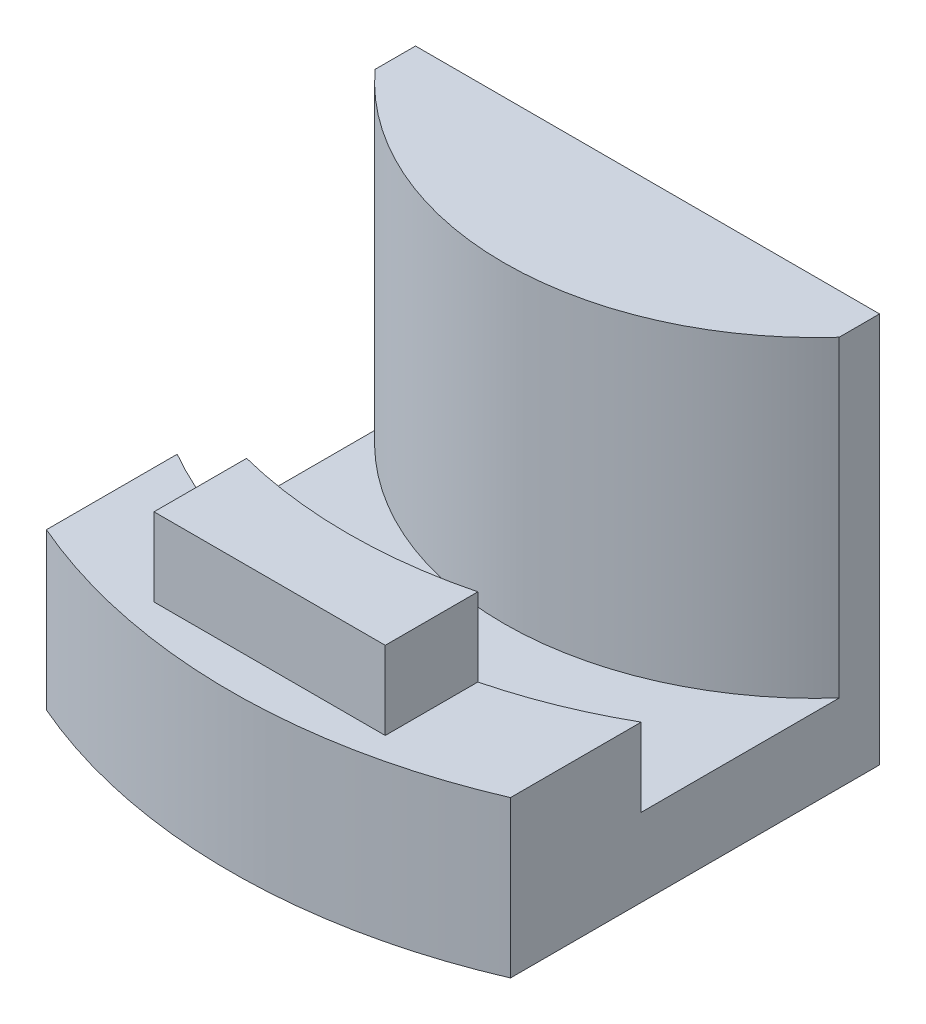
SolidWorks part; units mm, degrees
ref_plane "Front Plane" through (0, 0, 0) normal (0, 0, 1) x (1, 0, 0)
ref_plane "Top Plane" through (0, 0, 0) normal (0, 1, 0) x (1, 0, 0)
ref_plane "Right Plane" through (0, 0, 0) normal (1, 0, 0) x (0, 0, -1)
sketch "Sketch1" plane through (0, 0, 0) normal (0, 1, 0) x (1, 0, 0)
  circle A0 centre (0, 0) radius 38.1
  dimension "D1" = 76.2
extrude "Boss-Extrude1" add sketch "Sketch1" along normal blind 6.35
sketch "Sketch2" plane through (0, 6.35, 0) normal (0, 1, 0) x (1, 0, 0)
  circle A0 centre (0, 0) radius 25.4
  dimension "D1" = 50.8
extrude "Boss-Extrude2" add sketch "Sketch2" along normal blind 25.4
sketch "Sketch3" plane through (0, 0, 0) normal (0, 1, 0) x (1, 0, 0)
  circle A0 centre (0, 0) radius 47.625
  circle A1 centre (0, 0) radius 38.1
  dimension "D1" = 95.25
extrude "Boss-Extrude3" add sketch "Sketch3" along normal blind 12.7
sketch "Sketch4" plane through (0, 0, 0) normal (0, 1, 0) x (1, 0, 0)
  line L0 (-18.8595, -13.732) -> (18.8595, -13.732)
  line L1 (-47.625, 47.625) -> (-18.8595, 47.625)
  line L2 (-47.625, 47.625) -> (-47.625, -44.3219)
  line L3 (-47.625, -44.3219) -> (-18.8595, -44.3219)
  line L4 (-18.8595, -13.732) -> (-18.8595, -44.3219)
  line L5 (19.0079, 47.625) -> (47.625, 47.625)
  line L6 (18.8595, -13.732) -> (18.8595, -50.5738)
  line L7 (18.8595, -50.5738) -> (47.625, -50.5738)
  line L8 (47.625, 47.625) -> (47.625, -50.5738)
  line L9 (-18.8595, 47.625) -> (19.0079, 47.625)
  circle A0 centre (0, 0) radius 47.625 construction
  dimension "D1" = 37.719
  dimension "D2" = 18.8595
extrude "Cut-Extrude3" cut sketch "Sketch4" along normal through all
sketch "Sketch5" plane through (0, 12.7, 0) normal (0, 1, 0) x (1, 0, 0)
  line L1 (-9.398, -44.45) -> (9.398, -44.45)
  line L2 (-9.398, -44.45) -> (-9.398, -36.9227)
  line L4 (9.398, -44.45) -> (9.398, -36.9227)
  arc A0 (-18.8595, -33.1048) -> (18.8595, -33.1048) centre (0, 0) ccw construction
  arc A2 (-9.398, -36.9227) -> (9.398, -36.9227) centre (0, 0) ccw
  point P0 (0, -38.1)
  dimension "D1" = 18.796
  dimension "D2" = 6.35
  dimension "D3" = 9.398
extrude "Boss-Extrude4" add sketch "Sketch5" along normal blind 6.35
